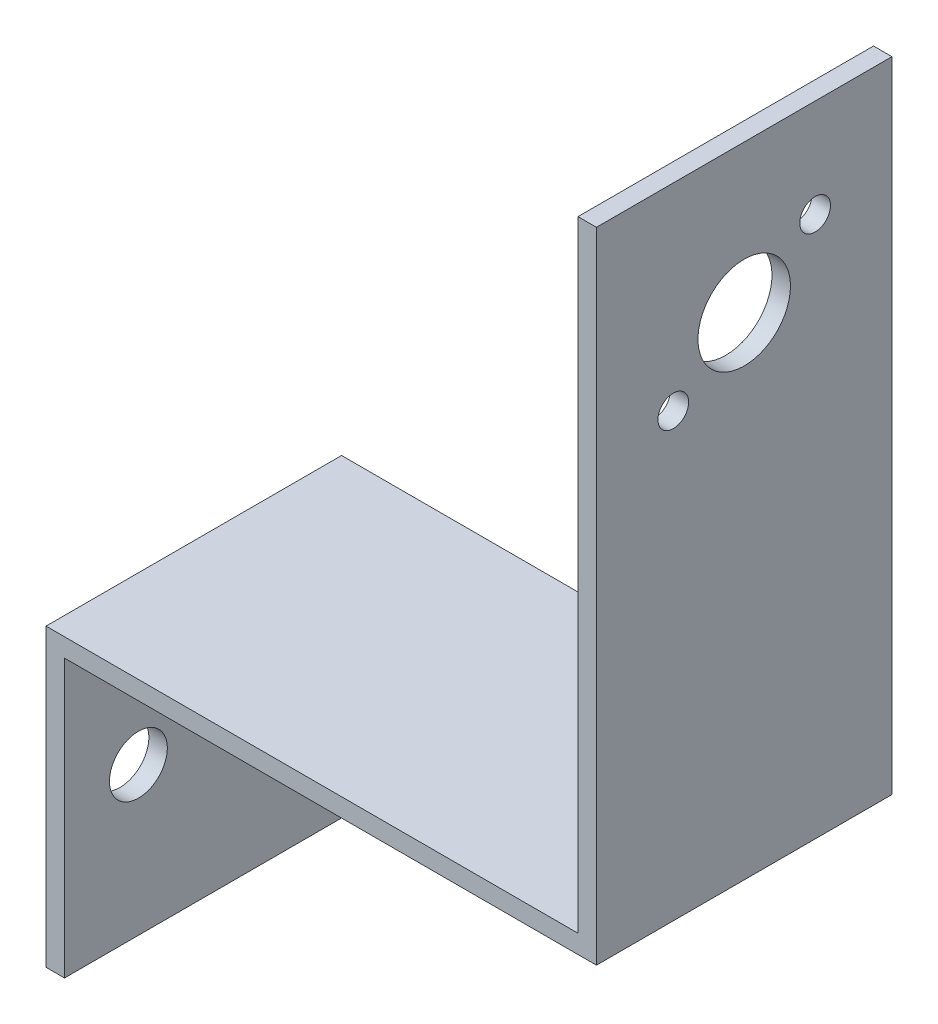
SolidWorks part; units mm, degrees
material "6061-T6 (SS)"
ref_plane "Front Plane" through (0, 0, 0) normal (0, 0, 1) x (1, 0, 0)
ref_plane "Top Plane" through (0, 0, 0) normal (0, 1, 0) x (1, 0, 0)
ref_plane "Right Plane" through (0, 0, 0) normal (1, 0, 0) x (0, 0, -1)
sketch "Sketch1" plane through (0, 0, 0) normal (0, 0, 1) x (1, 0, 0)
  line L0 (0, 0) -> (0, 25.4)
  line L1 (0, 25.4) -> (45.72, 25.4)
  line L2 (45.72, 25.4) -> (45.72, 78.74)
  dimension "D1" = 45.72
  dimension "D2" = 53.34
  dimension "D3" = 25.4
extrude "Extrude-Thin1" add sketch "Sketch1" along normal blind 25.4 thin
sketch "Sketch2" plane through (47.3075, 0, 0) normal (1, 0, 0) x (0, 0, -1)
  line L0 (-18.7963, 61.7713) -> (-6.6037, 70.3087) construction
  line L4 (-12.7, 66.04) -> (-25.4, 66.04) construction
  line L5 (-25.4, 23.8125) -> (-25.4, 78.74) construction
  line L6 (-25.4, 78.74) -> (0, 78.74) construction
  circle A0 centre (-12.7, 66.04) radius 3.9751
  circle A1 centre (-18.7963, 61.7713) radius 1.3208
  circle A2 centre (-6.6037, 70.3087) radius 1.3208
  point P8 (-12.7, 66.04)
  point P13 (-12.7, 78.74)
  dimension "D1" = 14.8844
  dimension "D2" = 2.6416
  dimension "D4" = 7.9502
  dimension "D3" = 35
  dimension "D5" = 12.7
extrude "Cut-Extrude1" cut sketch "Sketch2" against normal through all
sketch "Sketch3" plane through (1.5875, 0, 0) normal (1, 0, 0) x (0, 0, -1)
  line L0 (-25.4, 0) -> (0, 0) construction
  line L1 (-25.4, 0) -> (-25.4, 23.8125) construction
  line L2 (0, 0) -> (0, 23.8125) construction
  circle A0 centre (-19.05, 12.7) radius 2.4892
  circle A1 centre (-6.35, 12.7) radius 2.4892
  dimension "D1" = 4.9784
  dimension "D2" = 12.7
  dimension "D3" = 6.35
  dimension "D4" = 6.35
extrude "Cut-Extrude2" cut sketch "Sketch3" against normal through all
equation "\"Thick\"= \"in\""
